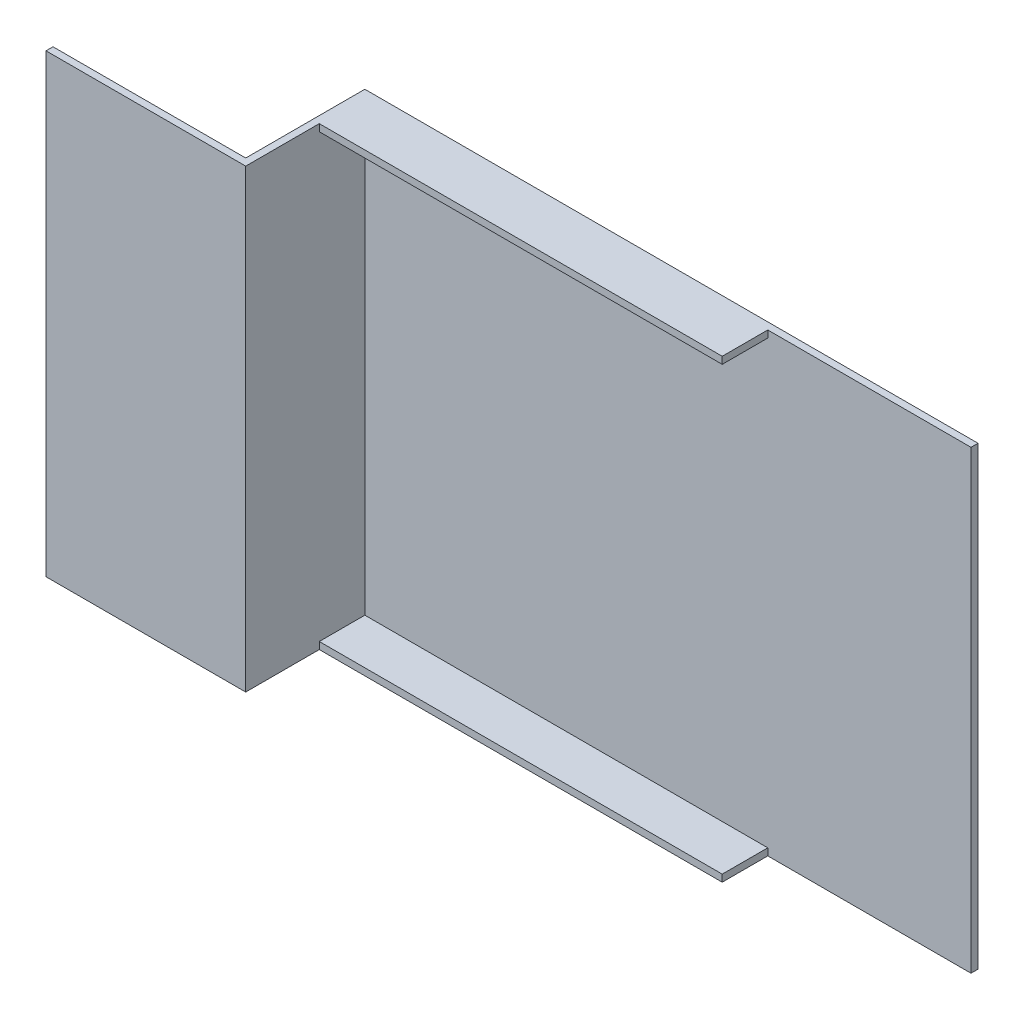
SolidWorks part; units mm, degrees
ref_plane "Front Plane" through (0, 0, 0) normal (0, 0, 1) x (1, 0, 0)
ref_plane "Top Plane" through (0, 0, 0) normal (0, 1, 0) x (1, 0, 0)
ref_plane "Right Plane" through (0, 0, 0) normal (1, 0, 0) x (0, 0, -1)
sketch "Sketch1" plane through (0, 0, 0) normal (0, 0, 1) x (1, 0, 0)
  line L1 (0, 0) -> (175, 0)
  line L2 (0, 0) -> (0, 130)
  line L3 (0, 130) -> (175, 130)
  line L4 (175, 0) -> (175, 130)
  dimension "D1" = 175
  dimension "D2" = 130
extrude "Boss-Extrude1" add sketch "Sketch1" along normal blind 2
sketch "Sketch2" plane through (0, 0, 2) normal (0, 0, 1) x (1, 0, 0)
  line L0 (0, 0) -> (175, 0) construction
  line L1 (0, 130) -> (2, 130)
  line L2 (0, 130) -> (0, 0)
  line L3 (0, 0) -> (2, 0)
  line L4 (2, 130) -> (2, 0)
  dimension "D1" = 2
extrude "Boss-Extrude2" add sketch "Sketch2" along normal blind 34
sketch "Sketch3" plane through (0, 0, 0) normal (-1, 0, 0) x (0, 0, 1)
  line L0 (36, 130) -> (0, 130) construction
  line L1 (36, 0) -> (34, 0)
  line L2 (36, 0) -> (36, 130)
  line L3 (36, 130) -> (34, 130)
  line L4 (34, 0) -> (34, 130)
  dimension "D1" = 2
extrude "Boss-Extrude4" add sketch "Sketch3" along normal blind 55
sketch "Sketch5" plane through (0, 0, 2) normal (0, 0, 1) x (1, 0, 0)
  line L0 (175, 130) -> (2, 130) construction
  line L1 (2, 0) -> (117, 0)
  line L2 (2, 0) -> (2, 2)
  line L3 (2, 2) -> (117, 2)
  line L4 (117, 0) -> (117, 2)
  line L6 (2, 130) -> (2, 128)
  line L7 (117, 130) -> (117, 128)
  line L8 (2, 130) -> (117, 130)
  line L9 (2, 128) -> (117, 128)
  dimension "D1" = 2
  dimension "D2" = 0
  dimension "D3" = 115
  dimension "D4" = 115
  dimension "D5" = 2
extrude "Boss-Extrude5" add sketch "Sketch5" along normal blind 13
